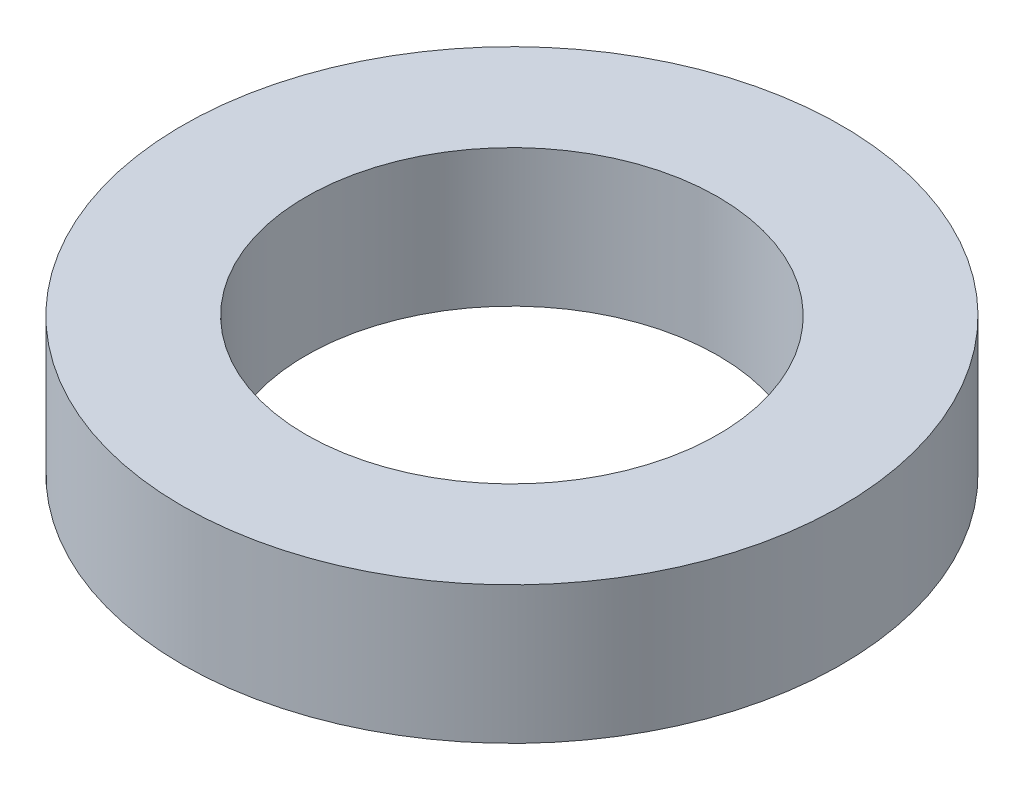
SolidWorks part; units mm, degrees
ref_plane "Front Plane" through (0, 0, 0) normal (0, 0, 1) x (1, 0, 0)
ref_plane "Top Plane" through (0, 0, 0) normal (0, 1, 0) x (1, 0, 0)
ref_plane "Right Plane" through (0, 0, 0) normal (1, 0, 0) x (0, 0, -1)
sketch "Sketch1" plane through (0, 0, 0) normal (0, 1, 0) x (1, 0, 0)
  circle A0 centre (0, 0) radius 7.5
  circle A1 centre (0, 0) radius 12
  dimension "D1" = 24
  dimension "D2" = 15
extrude "Boss-Extrude1" add sketch "Sketch1" along normal blind 5
